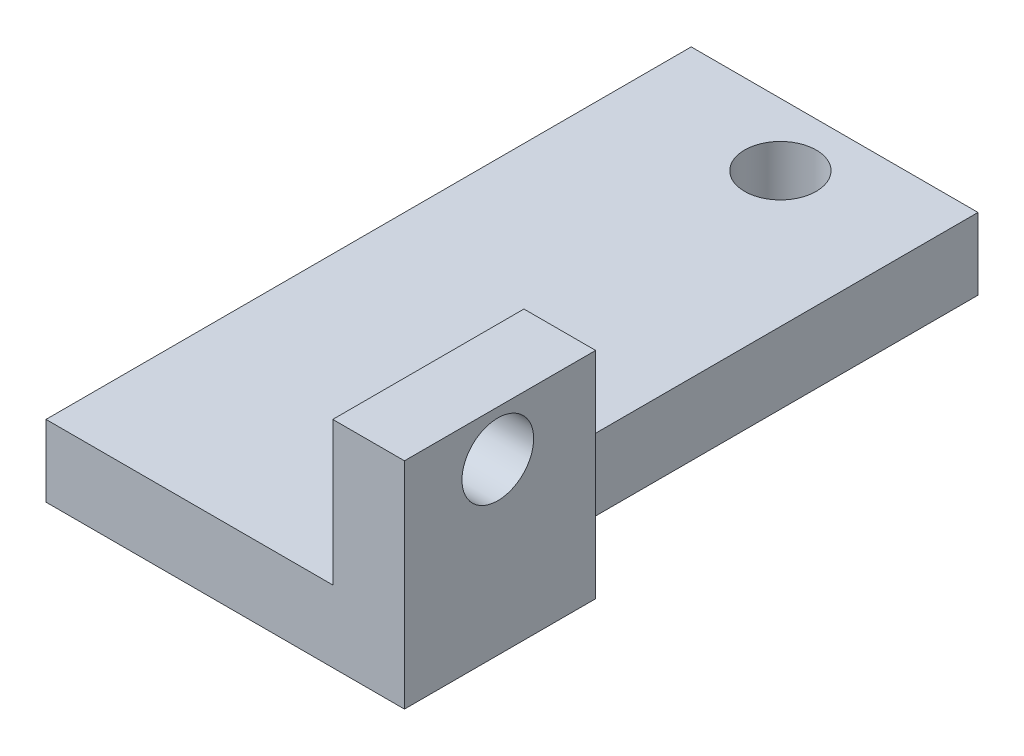
SolidWorks part; units mm, degrees
ref_plane "Alzado" through (0, 0, 0) normal (0, 0, 1) x (1, 0, 0)
ref_plane "Planta" through (0, 0, 0) normal (0, 1, 0) x (1, 0, 0)
ref_plane "Vista lateral" through (0, 0, 0) normal (1, 0, 0) x (0, 0, -1)
sketch "Croquis1" plane through (0, 0, 0) normal (0, 1, 0) x (1, 0, 0)
  line L1 (0, 0) -> (12, 0)
  line L2 (0, 0) -> (0, 27)
  line L3 (0, 27) -> (12, 27)
  line L4 (12, 0) -> (12, 27)
  circle A0 centre (6.3527, 24.3781) radius 1.5
  dimension "D1" = 27
  dimension "D2" = 12
extrude "Saliente-Extruir2" add sketch "Croquis1" along normal blind 3
sketch "Croquis6" plane through (12, 0, 0) normal (1, 0, 0) x (0, 0, -1)
  line L1 (0, 0) -> (8, 0)
  line L2 (0, 0) -> (0, 9)
  line L3 (0, 9) -> (8, 9)
  line L4 (8, 0) -> (8, 9)
  circle A0 centre (3.9058, 7.1003) radius 1.5
  dimension "D1" = 9
  dimension "D2" = 8
extrude "Saliente-Extruir4" add sketch "Croquis6" along normal blind 3
scale "Escala1" scale about centroid uniform scaling yes scale factor 7
